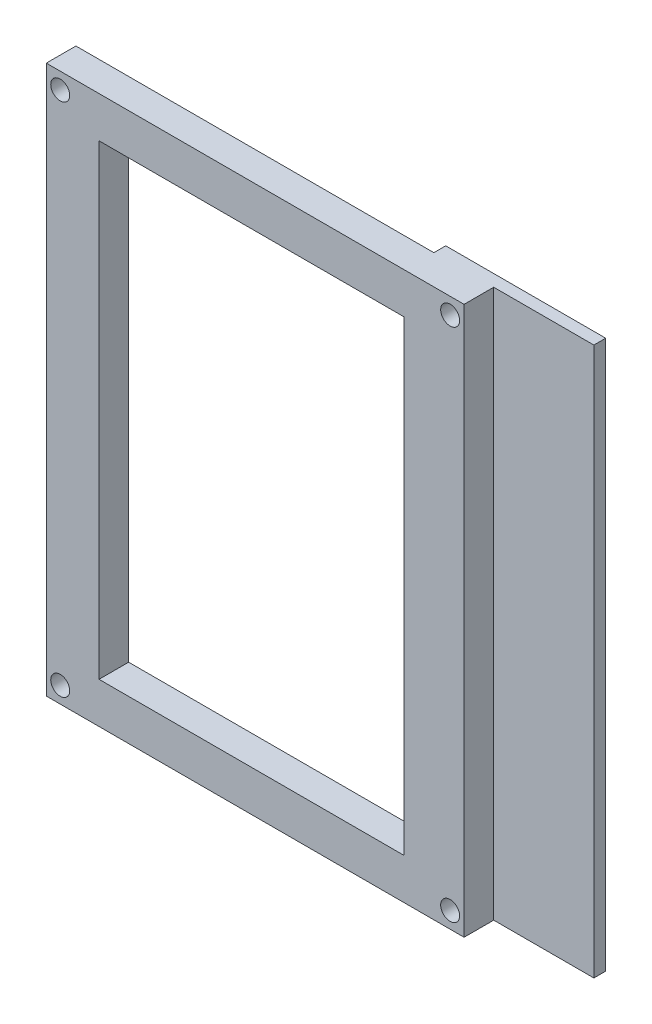
SolidWorks part; units mm, degrees
ref_plane "Спереди" through (0, 0, 0) normal (0, 0, 1) x (1, 0, 0)
ref_plane "Сверху" through (0, 0, 0) normal (0, 1, 0) x (1, 0, 0)
ref_plane "Справа" through (0, 0, 0) normal (1, 0, 0) x (0, 0, -1)
sketch "Эскиз1" plane through (0, 0, 28) normal (0, 0, -1) x (-1, 0, 0)
  line L4 (-4, 97.5) -> (-75, 97.5)
  line L5 (-75, 97.5) -> (-75, 4.5)
  line L6 (-75, 4.5) -> (-4, 4.5)
  line L7 (-4, 4.5) -> (-4, 97.5)
  line L8 (-4, 97.5) -> (-75, 97.5)
  line L9 (-75, 97.5) -> (-75, 4.5)
  line L10 (-75, 4.5) -> (-4, 4.5)
  line L11 (-4, 4.5) -> (-4, 97.5)
  line L12 (-13.4, 90.1) -> (-64.4, 90.1)
  line L13 (-64.4, 90.1) -> (-64.4, 11.9)
  line L14 (-64.4, 11.9) -> (-13.4, 11.9)
  line L15 (-13.4, 11.9) -> (-13.4, 90.1)
  line L16 (-13.4, 90.1) -> (-64.4, 90.1)
  line L17 (-64.4, 90.1) -> (-64.4, 11.9)
  line L18 (-64.4, 11.9) -> (-13.4, 11.9)
  line L19 (-13.4, 11.9) -> (-13.4, 90.1)
  circle A0 centre (-6.6, 7.5) radius 1.6 construction
  circle A1 centre (-6.6, 7.5) radius 1.6
  circle A2 centre (-72.4, 7.5) radius 1.6 construction
  circle A3 centre (-72.4, 7.5) radius 1.6
  circle A4 centre (-6.6, 94.5) radius 1.6 construction
  circle A5 centre (-6.6, 94.5) radius 1.6
  circle A6 centre (-72.4, 94.5) radius 1.6 construction
  circle A7 centre (-72.4, 94.5) radius 1.6
  dimension "D1" = 0
  dimension "D2" = 0
extrude "Бобышка-Вытянуть1" add sketch "Эскиз1" along normal blind 5
sketch "Эскиз2" plane through (0, 0, 28) normal (0, 0, 1) x (1, 0, 0)
  line L0 (4.25, 97.25) -> (74.75, 97.25)
  line L1 (4.25, 97.25) -> (4.25, 4.75)
  line L2 (74.75, 97.25) -> (74.75, 4.75)
  line L3 (4.25, 4.75) -> (74.75, 4.75)
  line L4 (75, 97.5) -> (75, 4.5) construction
  line L5 (75, 4.5) -> (4, 4.5) construction
  line L6 (4, 4.5) -> (4, 97.5) construction
  line L7 (4, 97.5) -> (75, 97.5) construction
  line L12 (4, 97.5) -> (4, 4.5)
  line L13 (4, 4.5) -> (75, 4.5)
  line L14 (75, 4.5) -> (75, 97.5)
  line L15 (75, 97.5) -> (4, 97.5)
  line L16 (4, 97.5) -> (4, 4.5)
  line L17 (4, 4.5) -> (75, 4.5)
  line L18 (75, 4.5) -> (75, 97.5)
  line L19 (75, 97.5) -> (4, 97.5)
  dimension "D1" = 0.25
  dimension "D2" = 0.25
  dimension "D3" = 0.25
  dimension "D4" = 0.25
  dimension "D5" = 0
extrude "Вырез-Вытянуть1" cut sketch "Эскиз2" against normal through all
sketch "Эскиз3" plane through (0, 0, 28) normal (0, 0, 1) x (1, 0, 0)
  line L0 (13.15, 90.35) -> (64.65, 90.35)
  line L1 (13.15, 90.35) -> (13.15, 11.65)
  line L2 (64.65, 90.35) -> (64.65, 11.65)
  line L3 (13.15, 11.65) -> (64.65, 11.65)
  line L4 (13.4, 90.1) -> (64.4, 90.1) construction
  line L5 (13.4, 11.9) -> (13.4, 90.1) construction
  line L6 (64.4, 90.1) -> (64.4, 11.9) construction
  line L7 (64.4, 11.9) -> (13.4, 11.9) construction
  line L8 (64.4, 11.9) -> (13.4, 11.9)
  line L9 (13.4, 11.9) -> (13.4, 90.1)
  line L10 (64.4, 90.1) -> (64.4, 11.9)
  line L11 (13.4, 90.1) -> (64.4, 90.1)
  dimension "D1" = 0.25
  dimension "D2" = 0.25
  dimension "D3" = 0.25
  dimension "D4" = 0.25
extrude "Вырез-Вытянуть2" cut sketch "Эскиз3" against normal through all
sketch "Эскиз5" plane through (0, 0, 23) normal (0, 0, -1) x (-1, 0, 0)
  line L0 (-64.65, 97.25) -> (-64.65, 4.75)
  line L1 (-64.65, 97.25) -> (-91.65, 97.25)
  line L2 (-64.65, 4.75) -> (-91.65, 4.75)
  line L3 (-91.65, 97.25) -> (-91.65, 4.75)
  line L4 (-74.75, 97.25) -> (-4.25, 97.25) construction
  line L5 (-4.25, 4.75) -> (-74.75, 4.75) construction
  line L6 (-64.65, 11.65) -> (-64.65, 90.35) construction
  circle A0 centre (-72.4, 94.5) radius 1.6 construction
  circle A1 centre (-72.4, 7.5) radius 1.6 construction
  circle A2 centre (-72.4, 94.5) radius 1.6
  circle A3 centre (-72.4, 7.5) radius 1.6
  dimension "D1" = 27
extrude "Бобышка-Вытянуть3" add sketch "Эскиз5" along normal blind 2
